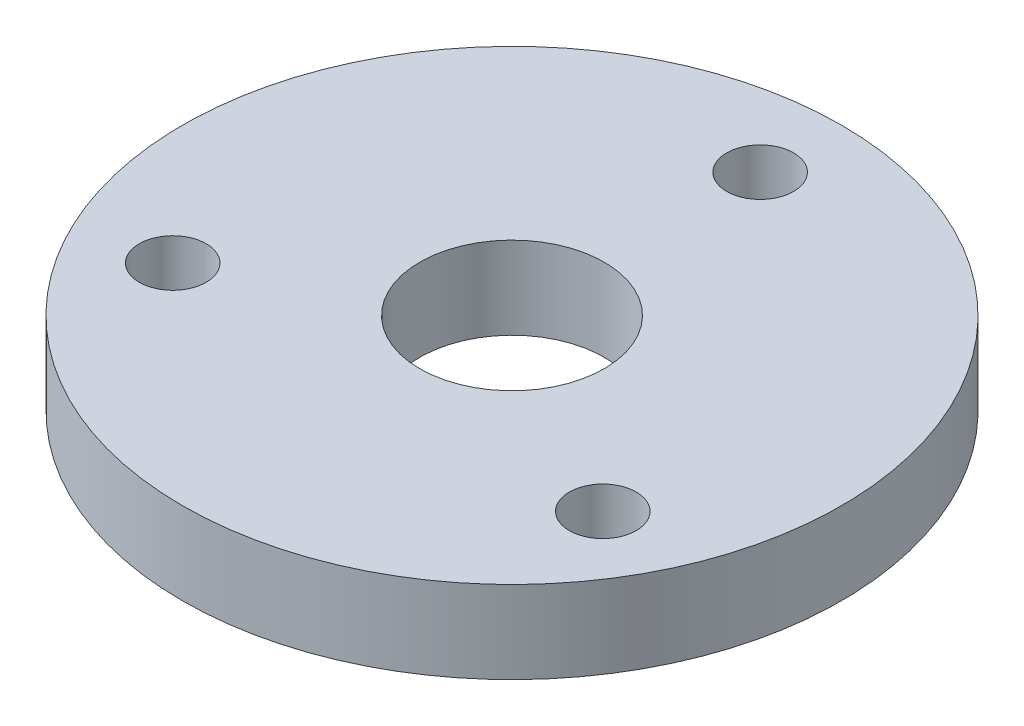
SolidWorks part; units mm, degrees
ref_plane "Front Plane" through (0, 0, 0) normal (0, 0, 1) x (1, 0, 0)
ref_plane "Top Plane" through (0, 0, 0) normal (0, 1, 0) x (1, 0, 0)
ref_plane "Right Plane" through (0, 0, 0) normal (1, 0, 0) x (0, 0, -1)
sketch "Sketch1" plane through (0, 0, 0) normal (0, 1, 0) x (1, 0, 0)
  line L0 (0, 0) -> (49.979, 0) construction
  line L1 (49.979, 0) -> (0, 0) construction
  line L2 (0, 0) -> (0, 44.401) construction
  circle A0 centre (0, 0) radius 28
  circle A1 centre (0, 0) radius 100
  circle A2 centre (0, 75.3) radius 10.15
  circle A3 centre (65.25, -37.7) radius 10.15
  circle A4 centre (-65.25, -37.7) radius 10.15
  point P10 (0, 0)
  point P13 (0, 0)
  point P14 (0, 0)
  dimension "D1" = 200
  dimension "D2" = 56
  dimension "D6" = 20.3
  dimension "D3" = 75.3
  dimension "D4" = 37.7
  dimension "D5" = 130.5
extrude "Boss-Extrude1" add sketch "Sketch1" along normal mid plane 25
